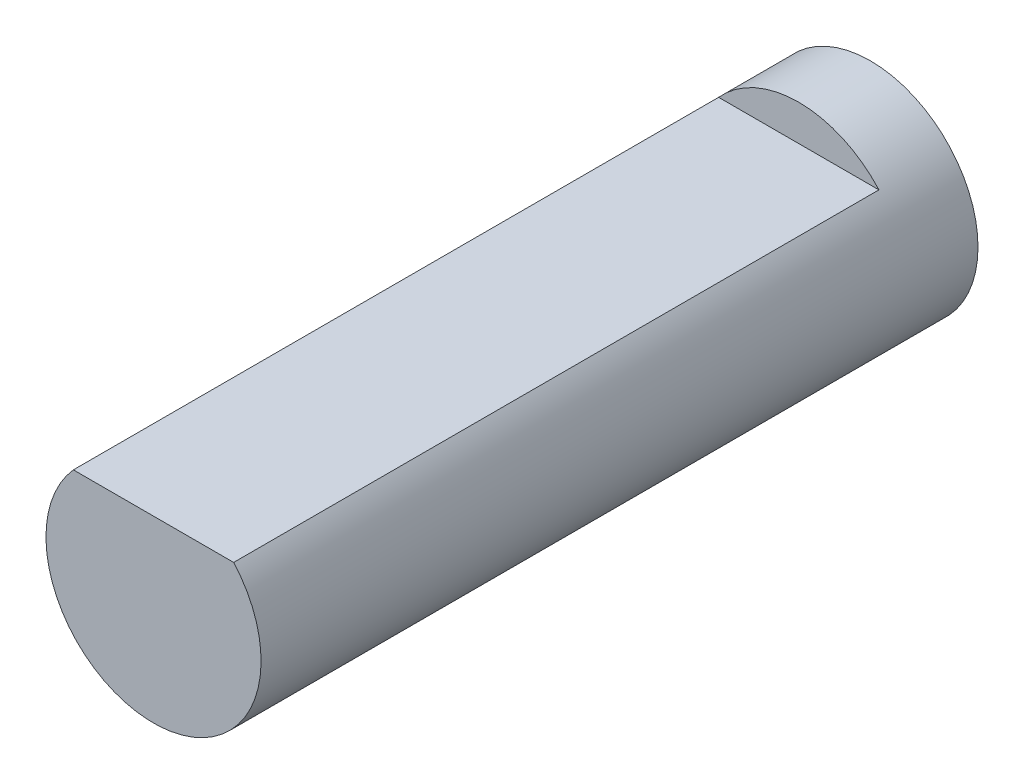
SolidWorks part; units mm, degrees
ref_plane "前视基准面" through (0, 0, 0) normal (0, 0, 1) x (1, 0, 0)
ref_plane "上视基准面" through (0, 0, 0) normal (0, 1, 0) x (1, 0, 0)
ref_plane "右视基准面" through (0, 0, 0) normal (1, 0, 0) x (0, 0, -1)
sketch "草图1" plane through (0, 0, 0) normal (0, 0, 1) x (1, 0, 0)
  circle A0 centre (0, 0) radius 1.5
extrude "凸台-拉伸1" add sketch "草图1" along normal blind 10
sketch "草图2" plane through (0, 0, 10) normal (0, 0, 1) x (1, 0, 0)
  line L1 (-1.118, 1) -> (1.118, 1)
  circle A0 centre (0, 0) radius 1.5 construction
  arc A1 (-1.118, 1) -> (1.118, 1) centre (0, 0) cw
extrude "切除-拉伸1" cut sketch "草图2" against normal blind 9
